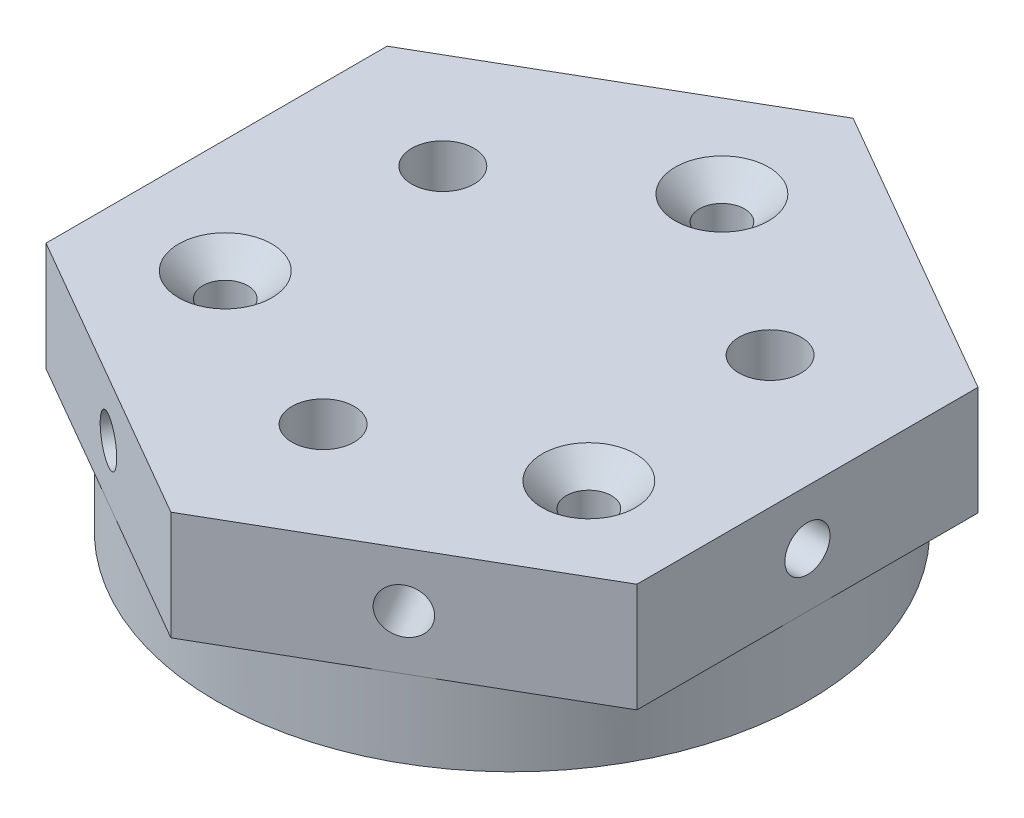
SolidWorks part; units mm, degrees
material "6061 合金"
ref_plane "前视基准面" through (0, 0, 0) normal (0, 0, 1) x (1, 0, 0)
ref_plane "上视基准面" through (0, 0, 0) normal (0, 1, 0) x (1, 0, 0)
ref_plane "右视基准面" through (0, 0, 0) normal (1, 0, 0) x (0, 0, -1)
sketch "草图1" plane through (0, 0, 0) normal (0, 1, 0) x (1, 0, 0)
  line L0 (0, 0) -> (0, 33.3478) construction
  line L1 (0, 0) -> (11.2563, 0) construction
  line B0 (-11.6913, -6.75) -> (0, 0) construction
  line B1 (0, 0) -> (11.6913, -6.75) construction
  line B2 (0, 0) -> (-10.5222, 6.075) construction
  line B3 (10.5222, 6.075) -> (0, 0) construction
  circle B4 centre (0, 0) radius 19
  circle B5 centre (0, 13.5) radius 1.45
  circle B6 centre (0, 0) radius 13.5 construction
  circle B7 centre (-11.6913, -6.75) radius 1.45
  circle B8 centre (11.6913, -6.75) radius 1.45
  circle B9 centre (0, 0) radius 12.15 construction
  circle B10 centre (-10.5222, 6.075) radius 2
  circle B11 centre (0, -12.15) radius 2
  circle B12 centre (10.5222, 6.075) radius 2
sketch_block_instance "块1-1"
sketch_block "块1" parameters "D1"=38, "D2"=27, "D3"=2.9, "D4"=24.3, "D5"=4
extrude "凸台-拉伸1" add sketch "草图1" along normal blind 12
sketch "草图2" plane through (0, 12, 0) normal (0, 1, 0) x (1, 0, 0)
  line L0 (0, 21.9393) -> (0, 0) construction
  line L1 (0, 21.9393) -> (-19, 10.9697)
  line L2 (-19, 10.9697) -> (-19, -10.9697)
  line L3 (-19, -10.9697) -> (0, -21.9393)
  line L4 (0, -21.9393) -> (19, -10.9697)
  line L5 (19, -10.9697) -> (19, 10.9697)
  line L6 (19, 10.9697) -> (0, 21.9393)
  circle A0 centre (0, 0) radius 19 construction
  circle A1 centre (0, 13.5) radius 1.45
  circle A2 centre (0, 13.5) radius 1.45 construction
  circle A3 centre (-10.5222, 6.075) radius 2
  circle A4 centre (-10.5222, 6.075) radius 2 construction
  circle A5 centre (10.5222, 6.075) radius 2
  circle A6 centre (10.5222, 6.075) radius 2 construction
  circle A7 centre (-11.6913, -6.75) radius 1.45
  circle A8 centre (-11.6913, -6.75) radius 1.45 construction
  circle A9 centre (0, -12.15) radius 2
  circle A10 centre (0, -12.15) radius 2 construction
  circle A11 centre (11.6913, -6.75) radius 1.45
  circle A12 centre (11.6913, -6.75) radius 1.45 construction
  dimension "D1" = 38
extrude "凸台-拉伸2" add sketch "草图2" against normal blind 7
sketch "草图3" plane through (9.5, 0, 16.4545) normal (0.5, 0, 0.866) x (0.866, 0, -0.5)
  line L1 (0, 12) -> (0, 5) construction
  line L2 (-10.9697, 12) -> (10.9697, 12) construction
  circle A1 centre (0, 8.5) radius 1.45
  dimension "D1" = 2.9
extrude "切除-拉伸1" cut sketch "草图3" against normal through all
sketch "草图4" plane through (-9.5, 0, 16.4545) normal (-0.5, 0, 0.866) x (0.866, 0, 0.5)
  line L0 (0, 5) -> (0, 12) construction
  line L1 (-10.9697, 12) -> (10.9697, 12) construction
  circle A0 centre (0, 8.5) radius 1.45
  dimension "D1" = 2.9
extrude "切除-拉伸2" cut sketch "草图4" against normal through all
sketch "草图5" plane through (-19, 0, 0) normal (-1, 0, 0) x (0, 0, 1)
  line L0 (0, 5) -> (0, 12) construction
  line L1 (-10.9697, 12) -> (10.9697, 12) construction
  circle A0 centre (0, 8.5) radius 1.45
  dimension "D1" = 2.9
extrude "切除-拉伸3" cut sketch "草图5" against normal blind 8
sketch "草图6" plane through (19, 0, 0) normal (1, 0, 0) x (0, 0, -1)
  line L0 (0, 12) -> (0, 5) construction
  line L1 (-10.9697, 12) -> (10.9697, 12) construction
  circle A0 centre (0, 8.5) radius 1.45
  dimension "D1" = 2.9
extrude "切除-拉伸4" cut sketch "草图6" against normal through all
chamfer "倒角1" distance 1.55 angle 45 3 edges at (0, 12, -12.05) (-11.6913, 12, 8.2) (11.6913, 12, 8.2)
